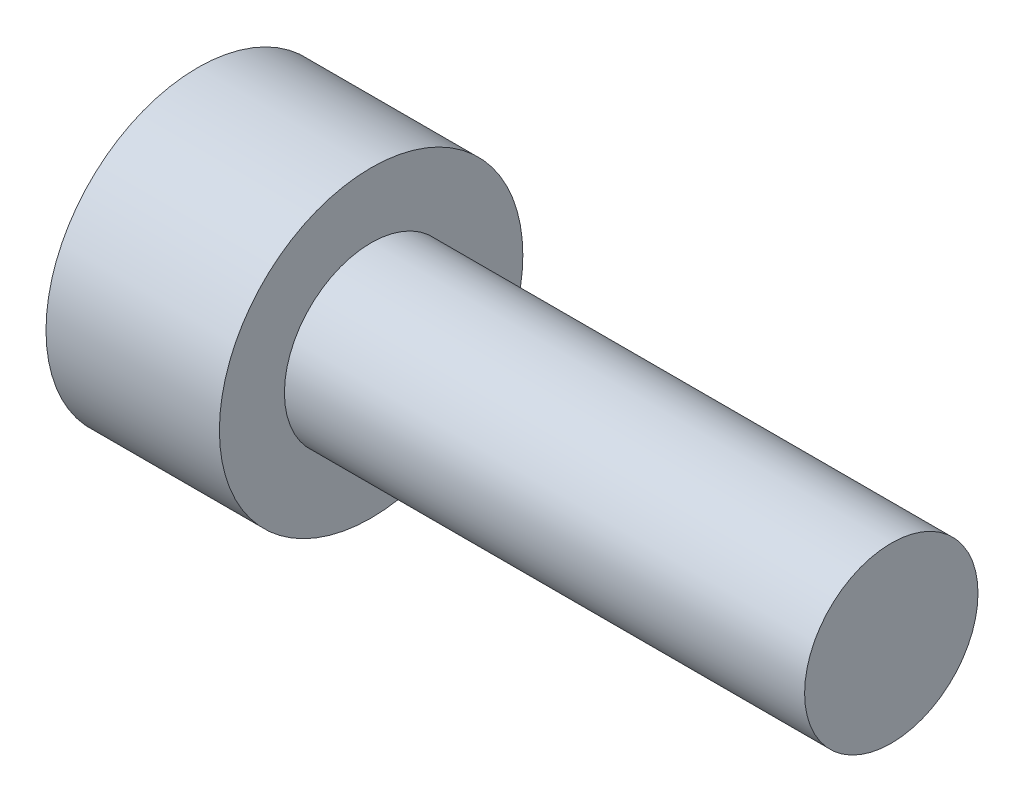
SolidWorks part; units mm, degrees
ref_plane "Płaszczyzna przednia" through (0, 0, 0) normal (0, 0, 1) x (1, 0, 0)
ref_plane "Płaszczyzna górna" through (0, 0, 0) normal (0, 1, 0) x (1, 0, 0)
ref_plane "Płaszczyzna prawa" through (0, 0, 0) normal (1, 0, 0) x (0, 0, -1)
sketch "Szkic1" plane through (0, 0, 0) normal (0, 0, 1) x (1, 0, 0)
  line L0 (0, 0) -> (0, 3.5)
  line L1 (0, 3.5) -> (4, 3.5)
  line L2 (4, 3.5) -> (4, 2)
  line L3 (4, 2) -> (16, 2)
  line L4 (16, 2) -> (16, 0)
  line L5 (16, 0) -> (0, 0)
  dimension "D1" = 4
  dimension "D2" = 12
  dimension "D3" = 2
  dimension "D4" = 3.5
revolve "Obrót1" add sketch "Szkic1" angle 360 about L5
cosmetic thread "Oznaczenie gwintu1" parameters "D2"=3.22
sketch "Szkic2" plane through (0, 0, 0) normal (-1, 0, 0) x (0, 0, 1)
  line L0 (-0.866, -1.5) -> (0.866, -1.5)
  line L7 (0.866, -1.5) -> (1.7321, 0)
  line L8 (1.7321, 0) -> (0.866, 1.5)
  line L9 (0.866, 1.5) -> (-0.866, 1.5)
  line L10 (-0.866, 1.5) -> (-1.7321, 0)
  line L11 (-1.7321, 0) -> (-0.866, -1.5)
  circle A0 centre (0, 0) radius 1.7321 construction
  dimension "D1" = 3
extrude "Wytnij-wyciągnięcie1" cut sketch "Szkic2" against normal blind 2
